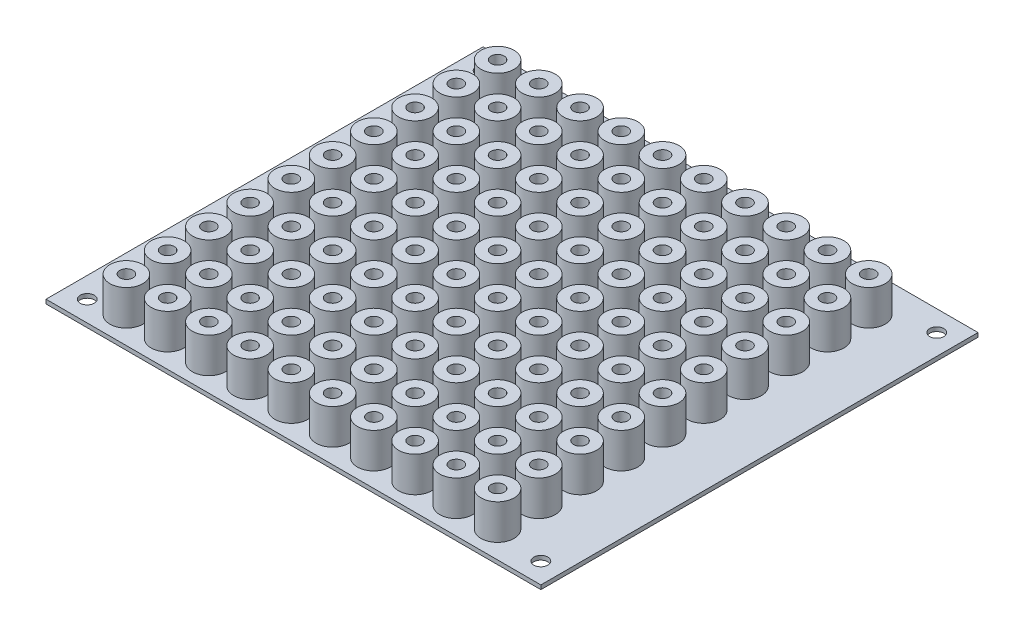
SolidWorks part; units mm, degrees
ref_plane "Front Plane" through (0, 0, 0) normal (0, 0, 1) x (1, 0, 0)
ref_plane "Top Plane" through (0, 0, 0) normal (0, 1, 0) x (1, 0, 0)
ref_plane "Right Plane" through (0, 0, 0) normal (1, 0, 0) x (0, 0, -1)
sketch "Sketch1" plane through (0, 0, 0) normal (0, 1, 0) x (1, 0, 0)
  line L0 (115, 101) -> (5, 101) construction
  line L1 (0, 0) -> (120, 0)
  line L2 (0, 0) -> (0, 106)
  line L3 (0, 106) -> (120, 106)
  line L4 (120, 0) -> (120, 106)
  line L6 (115, 101) -> (115, 5) construction
  circle A17 centre (13, 66.5) radius 1.25
  circle A18 centre (23, 66.5) radius 1.25
  circle A19 centre (13, 96.5) radius 1.25
  circle A28 centre (5, 5) radius 1.7
  circle A29 centre (5, 101) radius 1.7
  circle A30 centre (115, 101) radius 1.7
  circle A31 centre (115, 5) radius 1.7
  circle A32 centre (23, 96.5) radius 1.25
  circle A33 centre (33, 96.5) radius 1.25
  circle A34 centre (23, 86.5) radius 1.25
  circle A35 centre (33, 86.5) radius 1.25
  circle A36 centre (23, 76.5) radius 1.25
  circle A37 centre (33, 76.5) radius 1.25
  circle A38 centre (13, 86.5) radius 1.25
  circle A39 centre (13, 76.5) radius 1.25
  circle A40 centre (33, 66.5) radius 1.25
  circle A41 centre (13, 56.5) radius 1.25
  circle A42 centre (23, 56.5) radius 1.25
  circle A43 centre (33, 56.5) radius 1.25
  circle A44 centre (13, 46.5) radius 1.25
  circle A45 centre (23, 46.5) radius 1.25
  circle A46 centre (33, 46.5) radius 1.25
  circle A47 centre (13, 36.5) radius 1.25
  circle A48 centre (23, 36.5) radius 1.25
  circle A49 centre (33, 36.5) radius 1.25
  circle A50 centre (13, 26.5) radius 1.25
  circle A51 centre (23, 26.5) radius 1.25
  circle A52 centre (33, 26.5) radius 1.25
  circle A53 centre (13, 16.5) radius 1.25
  circle A54 centre (23, 16.5) radius 1.25
  circle A55 centre (33, 16.5) radius 1.25
  circle A56 centre (13, 6.5) radius 1.25
  circle A57 centre (23, 6.5) radius 1.25
  circle A58 centre (33, 6.5) radius 1.25
  circle A59 centre (43, 96.5) radius 1.25
  circle A60 centre (53, 96.5) radius 1.25
  circle A61 centre (63, 96.5) radius 1.25
  circle A62 centre (73, 96.5) radius 1.25
  circle A63 centre (83, 96.5) radius 1.25
  circle A64 centre (93, 96.5) radius 1.25
  circle A65 centre (103, 96.5) radius 1.25
  circle A66 centre (43, 86.5) radius 1.25
  circle A67 centre (53, 86.5) radius 1.25
  circle A68 centre (63, 86.5) radius 1.25
  circle A69 centre (73, 86.5) radius 1.25
  circle A70 centre (83, 86.5) radius 1.25
  circle A71 centre (93, 86.5) radius 1.25
  circle A72 centre (103, 86.5) radius 1.25
  circle A73 centre (43, 76.5) radius 1.25
  circle A74 centre (53, 76.5) radius 1.25
  circle A75 centre (63, 76.5) radius 1.25
  circle A76 centre (73, 76.5) radius 1.25
  circle A77 centre (83, 76.5) radius 1.25
  circle A78 centre (93, 76.5) radius 1.25
  circle A79 centre (103, 76.5) radius 1.25
  circle A80 centre (43, 66.5) radius 1.25
  circle A81 centre (53, 66.5) radius 1.25
  circle A82 centre (63, 66.5) radius 1.25
  circle A83 centre (73, 66.5) radius 1.25
  circle A84 centre (83, 66.5) radius 1.25
  circle A85 centre (93, 66.5) radius 1.25
  circle A86 centre (103, 66.5) radius 1.25
  circle A87 centre (43, 56.5) radius 1.25
  circle A88 centre (53, 56.5) radius 1.25
  circle A89 centre (63, 56.5) radius 1.25
  circle A90 centre (73, 56.5) radius 1.25
  circle A91 centre (83, 56.5) radius 1.25
  circle A92 centre (93, 56.5) radius 1.25
  circle A93 centre (103, 56.5) radius 1.25
  circle A94 centre (43, 46.5) radius 1.25
  circle A95 centre (53, 46.5) radius 1.25
  circle A96 centre (63, 46.5) radius 1.25
  circle A97 centre (73, 46.5) radius 1.25
  circle A98 centre (83, 46.5) radius 1.25
  circle A99 centre (93, 46.5) radius 1.25
  circle A100 centre (103, 46.5) radius 1.25
  circle A101 centre (43, 36.5) radius 1.25
  circle A102 centre (53, 36.5) radius 1.25
  circle A103 centre (63, 36.5) radius 1.25
  circle A104 centre (73, 36.5) radius 1.25
  circle A105 centre (83, 36.5) radius 1.25
  circle A106 centre (93, 36.5) radius 1.25
  circle A107 centre (103, 36.5) radius 1.25
  circle A108 centre (43, 26.5) radius 1.25
  circle A109 centre (53, 26.5) radius 1.25
  circle A110 centre (63, 26.5) radius 1.25
  circle A111 centre (73, 26.5) radius 1.25
  circle A112 centre (83, 26.5) radius 1.25
  circle A113 centre (93, 26.5) radius 1.25
  circle A114 centre (103, 26.5) radius 1.25
  circle A115 centre (43, 16.5) radius 1.25
  circle A116 centre (53, 16.5) radius 1.25
  circle A117 centre (63, 16.5) radius 1.25
  circle A118 centre (73, 16.5) radius 1.25
  circle A119 centre (83, 16.5) radius 1.25
  circle A120 centre (93, 16.5) radius 1.25
  circle A121 centre (103, 16.5) radius 1.25
  circle A122 centre (43, 6.5) radius 1.25
  circle A123 centre (53, 6.5) radius 1.25
  circle A124 centre (63, 6.5) radius 1.25
  circle A125 centre (73, 6.5) radius 1.25
  circle A126 centre (83, 6.5) radius 1.25
  circle A127 centre (93, 6.5) radius 1.25
  circle A128 centre (103, 6.5) radius 1.25
  point P7 (115, 53)
  point P8 (0, 0)
  point P9 (60, 101)
  point P10 (60, 106)
  point P11 (0, 0)
  point P20 (120, 53)
  dimension "D5" = 110
  dimension "D6" = 96
  dimension "D3" = 2.5
  dimension "D8" = 3.4
  dimension "D1" = 120
  dimension "D2" = 106
  dimension "D4" = 8
  dimension "D7" = 1.5
  dimension "D9" = 10
  dimension "D10" = 10
extrude "Boss-Extrude1" add sketch "Sketch1" along normal blind 1
sketch "Sketch2" plane through (0, 1, 0) normal (0, 1, 0) x (1, 0, 0)
  circle A0 centre (13, 96.5) radius 1.6
  circle A2 centre (13, 96.5) radius 4
  circle A3 centre (23, 96.5) radius 4
  circle A4 centre (23, 96.5) radius 1.6
  circle A5 centre (33, 96.5) radius 4
  circle A6 centre (33, 96.5) radius 1.6
  circle A7 centre (23, 86.5) radius 4
  circle A8 centre (23, 86.5) radius 1.6
  circle A9 centre (33, 86.5) radius 4
  circle A10 centre (33, 86.5) radius 1.6
  circle A11 centre (23, 76.5) radius 4
  circle A12 centre (23, 76.5) radius 1.6
  circle A13 centre (33, 76.5) radius 4
  circle A14 centre (33, 76.5) radius 1.6
  circle A15 centre (13, 86.5) radius 4
  circle A16 centre (13, 86.5) radius 1.6
  circle A17 centre (13, 76.5) radius 4
  circle A18 centre (13, 76.5) radius 1.6
  circle A19 centre (13, 66.5) radius 4
  circle A20 centre (13, 66.5) radius 1.6
  circle A21 centre (23, 66.5) radius 4
  circle A22 centre (23, 66.5) radius 1.6
  circle A23 centre (33, 66.5) radius 4
  circle A24 centre (33, 66.5) radius 1.6
  circle A25 centre (13, 56.5) radius 4
  circle A26 centre (13, 56.5) radius 1.6
  circle A27 centre (23, 56.5) radius 4
  circle A28 centre (23, 56.5) radius 1.6
  circle A29 centre (33, 56.5) radius 4
  circle A30 centre (33, 56.5) radius 1.6
  circle A31 centre (13, 46.5) radius 4
  circle A32 centre (13, 46.5) radius 1.6
  circle A33 centre (23, 46.5) radius 4
  circle A34 centre (23, 46.5) radius 1.6
  circle A35 centre (33, 46.5) radius 4
  circle A36 centre (33, 46.5) radius 1.6
  circle A37 centre (13, 36.5) radius 4
  circle A38 centre (13, 36.5) radius 1.6
  circle A39 centre (23, 36.5) radius 4
  circle A40 centre (23, 36.5) radius 1.6
  circle A41 centre (33, 36.5) radius 4
  circle A42 centre (33, 36.5) radius 1.6
  circle A43 centre (13, 26.5) radius 4
  circle A44 centre (13, 26.5) radius 1.6
  circle A45 centre (23, 26.5) radius 4
  circle A46 centre (23, 26.5) radius 1.6
  circle A47 centre (33, 26.5) radius 4
  circle A48 centre (33, 26.5) radius 1.6
  circle A49 centre (13, 16.5) radius 4
  circle A50 centre (13, 16.5) radius 1.6
  circle A51 centre (23, 16.5) radius 4
  circle A52 centre (23, 16.5) radius 1.6
  circle A53 centre (33, 16.5) radius 4
  circle A54 centre (33, 16.5) radius 1.6
  circle A55 centre (13, 6.5) radius 4
  circle A56 centre (13, 6.5) radius 1.6
  circle A57 centre (23, 6.5) radius 4
  circle A58 centre (23, 6.5) radius 1.6
  circle A59 centre (33, 6.5) radius 4
  circle A60 centre (33, 6.5) radius 1.6
  circle A61 centre (43, 96.5) radius 4
  circle A62 centre (43, 96.5) radius 1.6
  circle A63 centre (53, 96.5) radius 4
  circle A64 centre (53, 96.5) radius 1.6
  circle A65 centre (63, 96.5) radius 4
  circle A66 centre (63, 96.5) radius 1.6
  circle A67 centre (73, 96.5) radius 4
  circle A68 centre (73, 96.5) radius 1.6
  circle A69 centre (83, 96.5) radius 4
  circle A70 centre (83, 96.5) radius 1.6
  circle A71 centre (93, 96.5) radius 4
  circle A72 centre (93, 96.5) radius 1.6
  circle A73 centre (103, 96.5) radius 4
  circle A74 centre (103, 96.5) radius 1.6
  circle A75 centre (43, 86.5) radius 4
  circle A76 centre (43, 86.5) radius 1.6
  circle A77 centre (53, 86.5) radius 4
  circle A78 centre (53, 86.5) radius 1.6
  circle A79 centre (63, 86.5) radius 4
  circle A80 centre (63, 86.5) radius 1.6
  circle A81 centre (73, 86.5) radius 4
  circle A82 centre (73, 86.5) radius 1.6
  circle A83 centre (83, 86.5) radius 4
  circle A84 centre (83, 86.5) radius 1.6
  circle A85 centre (93, 86.5) radius 4
  circle A86 centre (93, 86.5) radius 1.6
  circle A87 centre (103, 86.5) radius 4
  circle A88 centre (103, 86.5) radius 1.6
  circle A89 centre (43, 76.5) radius 4
  circle A90 centre (43, 76.5) radius 1.6
  circle A91 centre (53, 76.5) radius 4
  circle A92 centre (53, 76.5) radius 1.6
  circle A93 centre (63, 76.5) radius 4
  circle A94 centre (63, 76.5) radius 1.6
  circle A95 centre (73, 76.5) radius 4
  circle A96 centre (73, 76.5) radius 1.6
  circle A97 centre (83, 76.5) radius 4
  circle A98 centre (83, 76.5) radius 1.6
  circle A99 centre (93, 76.5) radius 4
  circle A100 centre (93, 76.5) radius 1.6
  circle A101 centre (103, 76.5) radius 4
  circle A102 centre (103, 76.5) radius 1.6
  circle A103 centre (43, 66.5) radius 4
  circle A104 centre (43, 66.5) radius 1.6
  circle A105 centre (53, 66.5) radius 4
  circle A106 centre (53, 66.5) radius 1.6
  circle A107 centre (63, 66.5) radius 4
  circle A108 centre (63, 66.5) radius 1.6
  circle A109 centre (73, 66.5) radius 4
  circle A110 centre (73, 66.5) radius 1.6
  circle A111 centre (83, 66.5) radius 4
  circle A112 centre (83, 66.5) radius 1.6
  circle A113 centre (93, 66.5) radius 4
  circle A114 centre (93, 66.5) radius 1.6
  circle A115 centre (103, 66.5) radius 4
  circle A116 centre (103, 66.5) radius 1.6
  circle A117 centre (43, 56.5) radius 4
  circle A118 centre (43, 56.5) radius 1.6
  circle A119 centre (53, 56.5) radius 4
  circle A120 centre (53, 56.5) radius 1.6
  circle A121 centre (63, 56.5) radius 4
  circle A122 centre (63, 56.5) radius 1.6
  circle A123 centre (73, 56.5) radius 4
  circle A124 centre (73, 56.5) radius 1.6
  circle A125 centre (83, 56.5) radius 4
  circle A126 centre (83, 56.5) radius 1.6
  circle A127 centre (93, 56.5) radius 4
  circle A128 centre (93, 56.5) radius 1.6
  circle A129 centre (103, 56.5) radius 4
  circle A130 centre (103, 56.5) radius 1.6
  circle A131 centre (43, 46.5) radius 4
  circle A132 centre (43, 46.5) radius 1.6
  circle A133 centre (53, 46.5) radius 4
  circle A134 centre (53, 46.5) radius 1.6
  circle A135 centre (63, 46.5) radius 4
  circle A136 centre (63, 46.5) radius 1.6
  circle A137 centre (73, 46.5) radius 4
  circle A138 centre (73, 46.5) radius 1.6
  circle A139 centre (83, 46.5) radius 4
  circle A140 centre (83, 46.5) radius 1.6
  circle A141 centre (93, 46.5) radius 4
  circle A142 centre (93, 46.5) radius 1.6
  circle A143 centre (103, 46.5) radius 4
  circle A144 centre (103, 46.5) radius 1.6
  circle A145 centre (43, 36.5) radius 4
  circle A146 centre (43, 36.5) radius 1.6
  circle A147 centre (53, 36.5) radius 4
  circle A148 centre (53, 36.5) radius 1.6
  circle A149 centre (63, 36.5) radius 4
  circle A150 centre (63, 36.5) radius 1.6
  circle A151 centre (73, 36.5) radius 4
  circle A152 centre (73, 36.5) radius 1.6
  circle A153 centre (83, 36.5) radius 4
  circle A154 centre (83, 36.5) radius 1.6
  circle A155 centre (93, 36.5) radius 4
  circle A156 centre (93, 36.5) radius 1.6
  circle A157 centre (103, 36.5) radius 4
  circle A158 centre (103, 36.5) radius 1.6
  circle A159 centre (43, 26.5) radius 4
  circle A160 centre (43, 26.5) radius 1.6
  circle A161 centre (53, 26.5) radius 4
  circle A162 centre (53, 26.5) radius 1.6
  circle A163 centre (63, 26.5) radius 4
  circle A164 centre (63, 26.5) radius 1.6
  circle A165 centre (73, 26.5) radius 4
  circle A166 centre (73, 26.5) radius 1.6
  circle A167 centre (83, 26.5) radius 4
  circle A168 centre (83, 26.5) radius 1.6
  circle A169 centre (93, 26.5) radius 4
  circle A170 centre (93, 26.5) radius 1.6
  circle A171 centre (103, 26.5) radius 4
  circle A172 centre (103, 26.5) radius 1.6
  circle A173 centre (43, 16.5) radius 4
  circle A174 centre (43, 16.5) radius 1.6
  circle A175 centre (53, 16.5) radius 4
  circle A176 centre (53, 16.5) radius 1.6
  circle A177 centre (63, 16.5) radius 4
  circle A178 centre (63, 16.5) radius 1.6
  circle A179 centre (73, 16.5) radius 4
  circle A180 centre (73, 16.5) radius 1.6
  circle A181 centre (83, 16.5) radius 4
  circle A182 centre (83, 16.5) radius 1.6
  circle A183 centre (93, 16.5) radius 4
  circle A184 centre (93, 16.5) radius 1.6
  circle A185 centre (103, 16.5) radius 4
  circle A186 centre (103, 16.5) radius 1.6
  circle A187 centre (43, 6.5) radius 4
  circle A188 centre (43, 6.5) radius 1.6
  circle A189 centre (53, 6.5) radius 4
  circle A190 centre (53, 6.5) radius 1.6
  circle A191 centre (63, 6.5) radius 4
  circle A192 centre (63, 6.5) radius 1.6
  circle A193 centre (73, 6.5) radius 4
  circle A194 centre (73, 6.5) radius 1.6
  circle A195 centre (83, 6.5) radius 4
  circle A196 centre (83, 6.5) radius 1.6
  circle A197 centre (93, 6.5) radius 4
  circle A198 centre (93, 6.5) radius 1.6
  circle A199 centre (103, 6.5) radius 4
  circle A200 centre (103, 6.5) radius 1.6
  circle A201 centre (13, 96.5) radius 1.25 construction
  dimension "D1" = 3.2
  dimension "D2" = 8
  dimension "D3" = 10
  dimension "D4" = 10
extrude "Boss-Extrude2" add sketch "Sketch2" along normal blind 8.525
equation "\"o\"= 10mm"
equation "\"P\"= 10"
